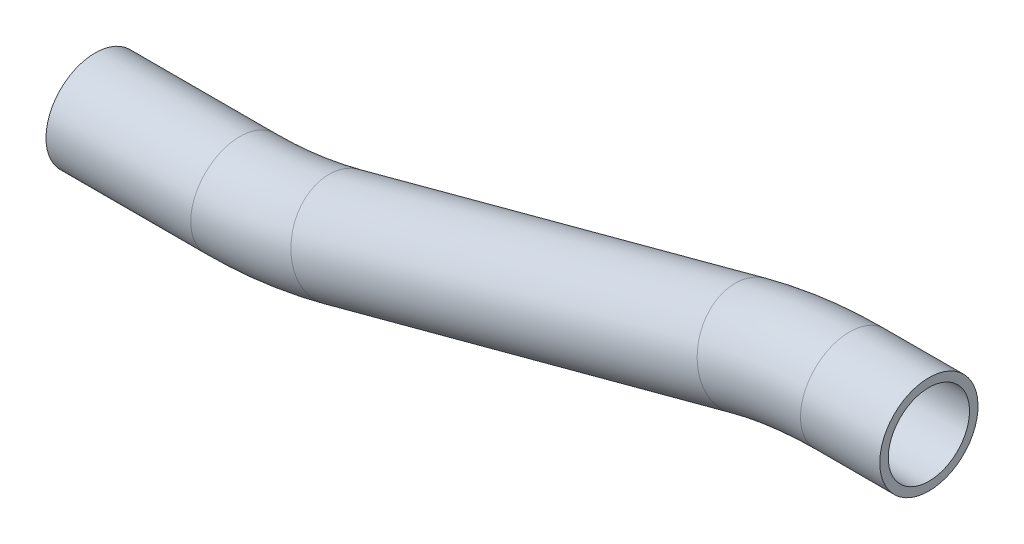
SolidWorks part; units mm, degrees
material "6061 Alloy"
ref_plane "Front Plane" through (0, 0, 0) normal (0, 0, 1) x (1, 0, 0)
ref_plane "Top Plane" through (0, 0, 0) normal (0, 1, 0) x (1, 0, 0)
ref_plane "Right Plane" through (0, 0, 0) normal (1, 0, 0) x (0, 0, -1)
sketch "Sketch1" plane through (0, 0, 0) normal (0, 0, 1) x (1, 0, 0)
  line L0 (0, 0) -> (15.3681, 0)
  line L2 (-19.722, -2.5965) -> (-98.4799, -23.6996)
  line L3 (-98.4799, -23.6996) -> (-10.0319, 0)
  line L4 (15.3681, 0) -> (-10.0319, 0)
  line L5 (-118.2019, -26.296) -> (-146.27, -26.296)
  line L6 (-146.27, -26.296) -> (-108.17, -26.296)
  line L7 (-19.722, -2.5965) -> (-108.17, -26.296)
  arc A0 (0, 0) -> (-19.722, -2.5965) centre (0, -76.2) ccw
  arc A1 (-98.4799, -23.6996) -> (-118.2019, -26.296) centre (-118.2019, 49.904) cw
  point P9 (-10.0319, 0)
  point P14 (-108.17, -26.296)
  dimension "D3" = 15
  dimension "D4" = 15
  dimension "D1" = 76.2
  dimension "D2" = 76.2
  dimension "D5" = 101.6
  dimension "D6" = 25.4
  dimension "D7" = 38.1
ref_plane "Plane1" through (15.3681, 0, 0) normal (-1, 0, 0) x (0, 0, 1)
sketch "Sketch2" plane through (15.3681, 0, 0) normal (-1, 0, 0) x (0, 0, 1)
  circle A0 centre (0, 0) radius 9.525
  circle A1 centre (0, 0) radius 7.874
  dimension "D1" = 19.05
  dimension "D2" = 15.748
sweep "Sweep1" add profiles "Sketch2" path "Sketch1"
